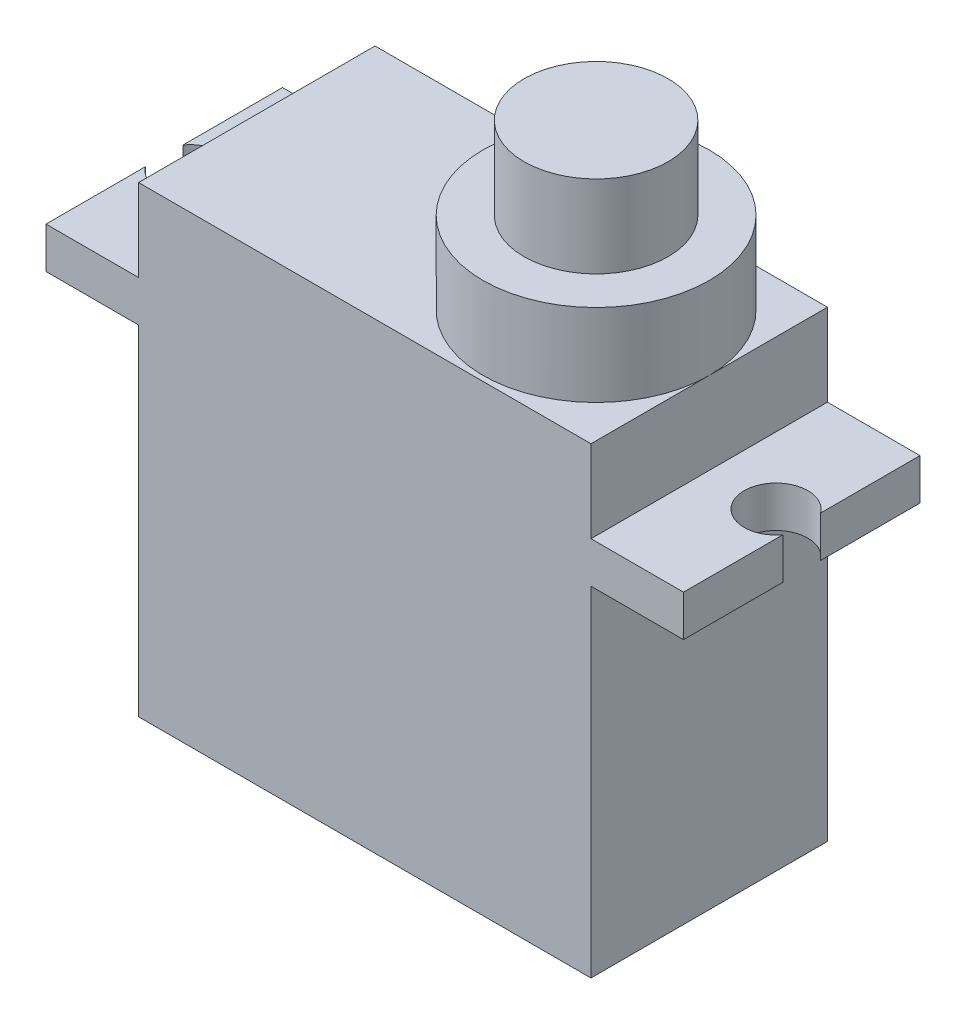
SolidWorks part; units mm, degrees
ref_plane "Front Plane" through (0, 0, 0) normal (0, 0, 1) x (1, 0, 0)
ref_plane "Top Plane" through (0, 0, 0) normal (0, 1, 0) x (1, 0, 0)
ref_plane "Right Plane" through (0, 0, 0) normal (1, 0, 0) x (0, 0, -1)
sketch "Sketch1" plane through (0, 0, 0) normal (0, 1, 0) x (1, 0, 0)
  line L0 (0, 16.773) -> (0, -16.7901) construction
  line L1 (-11, 5.75) -> (11, 5.75)
  line L2 (-11, 5.75) -> (-11, -5.75)
  line L3 (-11, -5.75) -> (11, -5.75)
  line L4 (11, 5.75) -> (11, -5.75)
  line L5 (-20.9372, 0) -> (19.3858, 0) construction
  dimension "D1" = 22
  dimension "D2" = 11.5
extrude "Boss-Extrude1" add sketch "Sketch1" along normal blind 16.5
sketch "Sketch2" plane through (0, 16.5, 0) normal (0, 1, 0) x (1, 0, 0)
  line L0 (0, 12.1606) -> (0, -13.204) construction
  line L1 (-15.5, 5.75) -> (15.5, 5.75)
  line L2 (-15.5, 5.75) -> (-15.5, 0.9165)
  line L3 (-15.5, -5.75) -> (15.5, -5.75)
  line L4 (15.5, 5.75) -> (15.5, 0.9165)
  line L5 (-20.5202, 0) -> (23.2529, 0) construction
  line L6 (11, 5.75) -> (-11, 5.75) construction
  line L7 (-15.5, -0.9165) -> (-15.5, -5.75)
  line L8 (15.5, -0.9165) -> (15.5, -5.75)
  arc A0 (-15.5, -0.9165) -> (-15.5, 0.9165) centre (-14.25, 0) ccw
  arc A1 (15.5, -0.9165) -> (15.5, 0.9165) centre (14.25, 0) cw
  dimension "D2" = 3.1
  dimension "D1" = 31
  dimension "D3" = 12.7
extrude "Boss-Extrude2" add sketch "Sketch2" along normal blind 2
sketch "Sketch4" plane through (0, 18.5, 0) normal (0, 1, 0) x (1, 0, 0)
  line L4 (-11, 5.75) -> (-11, -5.75)
  line L5 (11, 5.75) -> (-11, 5.75)
  line L18 (11, -5.75) -> (11, 5.75)
  line L19 (-11, -5.75) -> (11, -5.75)
  line L20 (-11, 5.75) -> (-11, -5.75)
  line L21 (11, 5.75) -> (-11, 5.75)
  line L22 (11, -5.75) -> (11, 5.75)
  line L23 (-11, -5.75) -> (11, -5.75)
  dimension "D2" = 0
extrude "Boss-Extrude3" add sketch "Sketch4" along normal blind 4
sketch "Sketch5" plane through (0, 22.5, 0) normal (0, 1, 0) x (1, 0, 0)
  line L0 (11, -5.75) -> (11, 5.75) construction
  line L1 (-15.5784, 0) -> (19.468, 0) construction
  circle A0 centre (5.5, 0) radius 5.5
  dimension "D1" = 11
extrude "Boss-Extrude4" add sketch "Sketch5" along normal blind 4
sketch "Sketch7" plane through (0, 26.5, 0) normal (0, 1, 0) x (1, 0, 0)
  line L1 (11, 0) -> (11, 5.75) construction
  line L2 (0, 0) -> (20.8555, 0) construction
  circle A0 centre (5.5, 0) radius 3.5
  dimension "D1" = 7
  dimension "D2" = 5.5
extrude "Boss-Extrude5" add sketch "Sketch7" along normal blind 4
